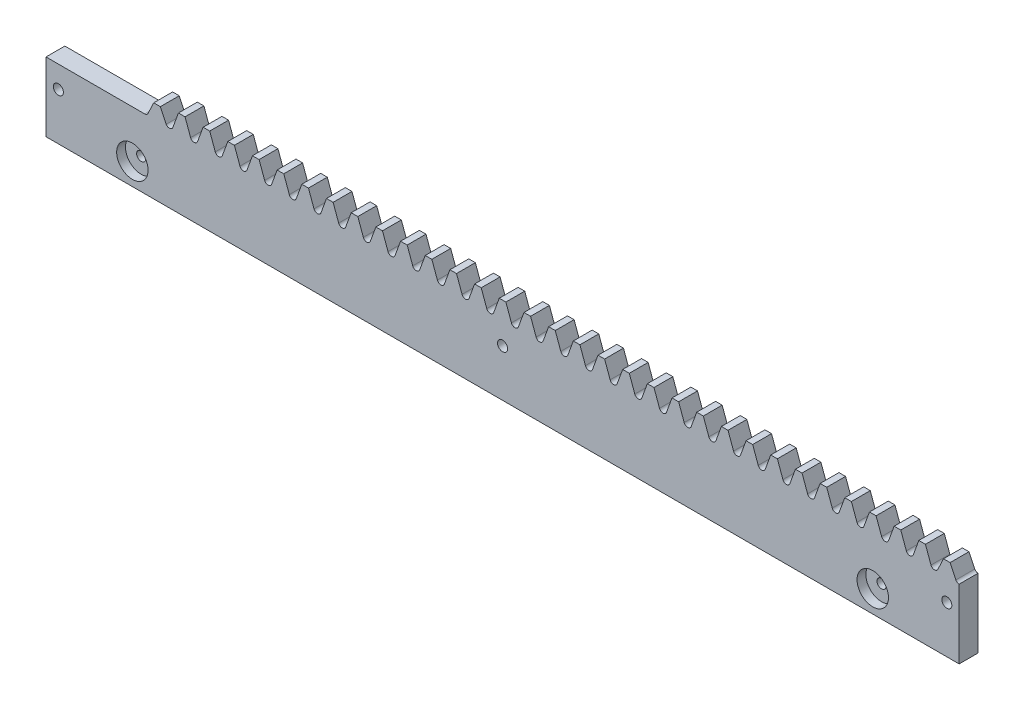
SolidWorks part; units mm, degrees
ref_plane "Plane1" through (0, 0, 0) normal (0, 0, 1) x (1, 0, 0)
ref_plane "Plane2" through (0, 0, 0) normal (0, 1, 0) x (1, 0, 0)
ref_plane "Plane3" through (0, 0, 0) normal (1, 0, 0) x (0, 0, -1)
sketch "Esquisse1" plane through (0, 0, 0) normal (0, 0, 1) x (1, 0, 0)
  line L0 (-11.781, 22) -> (19.635, 22)
  line L1 (23.5619, 29.1362) -> (23.5619, 19.2192) construction
  line L2 (-16.2297, 22) -> (24.6155, 22) construction
  line L3 (18.2522, 26.5) -> (283.3605, 26.5) construction
  line L4 (22.5084, 28.8854) -> (22.5084, 23.1798) construction
  line L5 (22.5084, 26.5) -> (20.6365, 22.5562)
  line L6 (24.6155, 26.5) -> (26.4874, 22.5562)
  line L7 (-29.4776, 0) -> (286.0574, 0) construction
  line L8 (22.5084, 26.5) -> (24.6155, 26.5)
  line L10 (275.9429, 26.742) -> (275.9429, 19.9201) construction
  line L11 (273.8358, 26.742) -> (273.8358, 19.9201) construction
  line L12 (273.8358, 26.5) -> (272.0069, 22.6314)
  line L13 (275.9429, 26.5) -> (277.7718, 22.6314)
  line L14 (273.8358, 26.5) -> (275.9429, 26.5)
  line L20 (28.5976, 22.7763) -> (30.3624, 27.625)
  line L21 (30.3624, 27.625) -> (32.4695, 27.625)
  line L22 (34.2343, 22.7763) -> (32.4695, 27.625)
  line L23 (36.4515, 22.7763) -> (38.2163, 27.625)
  line L24 (38.2163, 27.625) -> (40.3235, 27.625)
  line L25 (42.0883, 22.7763) -> (40.3235, 27.625)
  line L26 (44.3055, 22.7763) -> (46.0703, 27.625)
  line L27 (46.0703, 27.625) -> (48.1775, 27.625)
  line L28 (49.9423, 22.7763) -> (48.1775, 27.625)
  line L29 (52.1595, 22.7763) -> (53.9243, 27.625)
  line L30 (53.9243, 27.625) -> (56.0314, 27.625)
  line L31 (57.7962, 22.7763) -> (56.0314, 27.625)
  line L32 (60.0135, 22.7763) -> (61.7783, 27.625)
  line L33 (61.7783, 27.625) -> (63.8854, 27.625)
  line L34 (65.6502, 22.7763) -> (63.8854, 27.625)
  line L35 (67.8675, 22.7763) -> (69.6323, 27.625)
  line L36 (69.6323, 27.625) -> (71.7394, 27.625)
  line L37 (73.5042, 22.7763) -> (71.7394, 27.625)
  line L38 (75.7215, 22.7763) -> (77.4862, 27.625)
  line L39 (77.4862, 27.625) -> (79.5934, 27.625)
  line L40 (81.3582, 22.7763) -> (79.5934, 27.625)
  line L41 (83.5754, 22.7763) -> (85.3402, 27.625)
  line L42 (85.3402, 27.625) -> (87.4474, 27.625)
  line L43 (89.2122, 22.7763) -> (87.4474, 27.625)
  line L44 (91.4294, 22.7763) -> (93.1942, 27.625)
  line L45 (93.1942, 27.625) -> (95.3013, 27.625)
  line L46 (97.0661, 22.7763) -> (95.3013, 27.625)
  line L47 (99.2834, 22.7763) -> (101.0482, 27.625)
  line L48 (101.0482, 27.625) -> (103.1553, 27.625)
  line L49 (104.9201, 22.7763) -> (103.1553, 27.625)
  line L50 (107.1374, 22.7763) -> (108.9022, 27.625)
  line L51 (108.9022, 27.625) -> (111.0093, 27.625)
  line L52 (112.7741, 22.7763) -> (111.0093, 27.625)
  line L53 (114.9914, 22.7763) -> (116.7562, 27.625)
  line L54 (116.7562, 27.625) -> (118.8633, 27.625)
  line L55 (120.6281, 22.7763) -> (118.8633, 27.625)
  line L56 (122.8453, 22.7763) -> (124.6101, 27.625)
  line L57 (124.6101, 27.625) -> (126.7173, 27.625)
  line L58 (128.4821, 22.7763) -> (126.7173, 27.625)
  line L59 (130.6993, 22.7763) -> (132.4641, 27.625)
  line L60 (132.4641, 27.625) -> (134.5713, 27.625)
  line L61 (136.3361, 22.7763) -> (134.5713, 27.625)
  line L62 (138.5533, 22.7763) -> (140.3181, 27.625)
  line L63 (140.3181, 27.625) -> (142.4252, 27.625)
  line L64 (144.19, 22.7763) -> (142.4252, 27.625)
  line L65 (146.4073, 22.7763) -> (148.1721, 27.625)
  line L66 (148.1721, 27.625) -> (150.2792, 27.625)
  line L67 (152.044, 22.7763) -> (150.2792, 27.625)
  line L68 (154.2613, 22.7763) -> (156.0261, 27.625)
  line L69 (156.0261, 27.625) -> (158.1332, 27.625)
  line L70 (159.898, 22.7763) -> (158.1332, 27.625)
  line L71 (162.1153, 22.7763) -> (163.88, 27.625)
  line L72 (163.88, 27.625) -> (165.9872, 27.625)
  line L73 (167.752, 22.7763) -> (165.9872, 27.625)
  line L74 (169.9692, 22.7763) -> (171.734, 27.625)
  line L75 (171.734, 27.625) -> (173.8412, 27.625)
  line L76 (175.606, 22.7763) -> (173.8412, 27.625)
  line L77 (177.8232, 22.7763) -> (179.588, 27.625)
  line L78 (179.588, 27.625) -> (181.6951, 27.625)
  line L79 (183.4599, 22.7763) -> (181.6951, 27.625)
  line L80 (185.6772, 22.7763) -> (187.442, 27.625)
  line L81 (187.442, 27.625) -> (189.5491, 27.625)
  line L82 (191.3139, 22.7763) -> (189.5491, 27.625)
  line L83 (193.5312, 22.7763) -> (195.296, 27.625)
  line L84 (195.296, 27.625) -> (197.4031, 27.625)
  line L85 (199.1679, 22.7763) -> (197.4031, 27.625)
  line L86 (201.3852, 22.7763) -> (203.15, 27.625)
  line L87 (203.15, 27.625) -> (205.2571, 27.625)
  line L88 (207.0219, 22.7763) -> (205.2571, 27.625)
  line L89 (209.2391, 22.7763) -> (211.0039, 27.625)
  line L90 (211.0039, 27.625) -> (213.1111, 27.625)
  line L91 (214.8759, 22.7763) -> (213.1111, 27.625)
  line L92 (217.0931, 22.7763) -> (218.8579, 27.625)
  line L93 (218.8579, 27.625) -> (220.9651, 27.625)
  line L94 (222.7298, 22.7763) -> (220.9651, 27.625)
  line L95 (224.9471, 22.7763) -> (226.7119, 27.625)
  line L96 (226.7119, 27.625) -> (228.819, 27.625)
  line L97 (230.5838, 22.7763) -> (228.819, 27.625)
  line L98 (232.8011, 22.7763) -> (234.5659, 27.625)
  line L99 (234.5659, 27.625) -> (236.673, 27.625)
  line L100 (238.4378, 22.7763) -> (236.673, 27.625)
  line L101 (240.6551, 22.7763) -> (242.4199, 27.625)
  line L102 (242.4199, 27.625) -> (244.527, 27.625)
  line L103 (246.2918, 22.7763) -> (244.527, 27.625)
  line L104 (248.509, 22.7763) -> (250.2738, 27.625)
  line L105 (250.2738, 27.625) -> (252.381, 27.625)
  line L106 (254.1458, 22.7763) -> (252.381, 27.625)
  line L107 (256.363, 22.7763) -> (258.1278, 27.625)
  line L108 (258.1278, 27.625) -> (260.235, 27.625)
  line L109 (261.9998, 22.7763) -> (260.235, 27.625)
  line L110 (264.217, 22.7763) -> (265.9818, 27.625)
  line L111 (265.9818, 27.625) -> (268.0889, 27.625)
  line L112 (269.8537, 22.7763) -> (268.0889, 27.625)
  line L113 (-11.781, 27.0667) -> (-11.781, -40.6674) construction
  line L114 (19.635, 37.0607) -> (19.635, -15.8181) construction
  line L115 (283.3605, 22) -> (228.0591, 22) construction
  line L116 (278.8163, 26.742) -> (278.8163, -7.4189) construction
  line L118 (-11.781, 22) -> (-11.781, 0)
  line L121 (278.8163, 22) -> (278.8163, 0)
  line L131 (278.8163, 0) -> (-11.781, 0)
  line L132 (133.5177, 28.2837) -> (133.5177, 9.5143) construction
  line L133 (130.5371, 22) -> (141.4123, 22) construction
  line L134 (-45.8284, 15) -> (286.0574, 15) construction
  line L135 (-7.854, 23.9583) -> (-7.854, 12.1613) construction
  line L136 (274.8894, 25.9335) -> (274.8894, 12.5592) construction
  line L137 (-2.8184, 22.7763) -> (-1.0536, 27.625) [skipped]
  line L138 (-1.0536, 27.625) -> (1.0536, 27.625) [skipped]
  line L139 (2.8184, 22.7763) -> (1.0536, 27.625) [skipped]
  line L140 (5.0356, 22.7763) -> (6.8004, 27.625) [skipped]
  line L141 (6.8004, 27.625) -> (8.9076, 27.625) [skipped]
  line L142 (10.6723, 22.7763) -> (8.9076, 27.625) [skipped]
  line L143 (12.8896, 22.7763) -> (14.6544, 27.625) [skipped]
  line L144 (14.6544, 27.625) -> (16.7615, 27.625) [skipped]
  line L145 (18.5263, 22.7763) -> (16.7615, 27.625) [skipped]
  line L146 (22.5084, 27.625) -> (24.6155, 27.625) [skipped]
  line L147 (26.3803, 22.7763) -> (24.6155, 27.625) [skipped]
  line L148 (20.7436, 22.7763) -> (22.5084, 27.625) [skipped]
  line L149 (273.8358, 27.625) -> (275.9429, 27.625) [skipped]
  line L150 (277.7077, 22.7763) -> (275.9429, 27.625) [skipped]
  line L151 (272.071, 22.7763) -> (273.8358, 27.625) [skipped]
  arc A7 (19.635, 22) -> (20.6365, 22.5562) centre (19.635, 23.1798) ccw
  arc A8 (27.4889, 22) -> (26.4874, 22.5562) centre (27.4889, 23.1798) cw
  arc A9 (27.4889, 22) -> (28.5976, 22.7763) centre (27.4889, 23.1798) ccw
  arc A10 (35.3429, 22) -> (34.2343, 22.7763) centre (35.3429, 23.1798) cw
  arc A11 (35.3429, 22) -> (36.4515, 22.7763) centre (35.3429, 23.1798) ccw
  arc A12 (43.1969, 22) -> (42.0883, 22.7763) centre (43.1969, 23.1798) cw
  arc A13 (43.1969, 22) -> (44.3055, 22.7763) centre (43.1969, 23.1798) ccw
  arc A14 (51.0509, 22) -> (49.9423, 22.7763) centre (51.0509, 23.1798) cw
  arc A15 (51.0509, 22) -> (52.1595, 22.7763) centre (51.0509, 23.1798) ccw
  arc A16 (58.9049, 22) -> (57.7962, 22.7763) centre (58.9049, 23.1798) cw
  arc A17 (58.9049, 22) -> (60.0135, 22.7763) centre (58.9049, 23.1798) ccw
  arc A18 (66.7588, 22) -> (65.6502, 22.7763) centre (66.7588, 23.1798) cw
  arc A19 (66.7588, 22) -> (67.8675, 22.7763) centre (66.7588, 23.1798) ccw
  arc A20 (74.6128, 22) -> (73.5042, 22.7763) centre (74.6128, 23.1798) cw
  arc A21 (74.6128, 22) -> (75.7215, 22.7763) centre (74.6128, 23.1798) ccw
  arc A22 (82.4668, 22) -> (81.3582, 22.7763) centre (82.4668, 23.1798) cw
  arc A23 (82.4668, 22) -> (83.5754, 22.7763) centre (82.4668, 23.1798) ccw
  arc A24 (90.3208, 22) -> (89.2122, 22.7763) centre (90.3208, 23.1798) cw
  arc A25 (90.3208, 22) -> (91.4294, 22.7763) centre (90.3208, 23.1798) ccw
  arc A26 (98.1748, 22) -> (97.0661, 22.7763) centre (98.1748, 23.1798) cw
  arc A27 (98.1748, 22) -> (99.2834, 22.7763) centre (98.1748, 23.1798) ccw
  arc A28 (106.0288, 22) -> (104.9201, 22.7763) centre (106.0288, 23.1798) cw
  arc A29 (106.0288, 22) -> (107.1374, 22.7763) centre (106.0288, 23.1798) ccw
  arc A30 (113.8827, 22) -> (112.7741, 22.7763) centre (113.8827, 23.1798) cw
  arc A31 (113.8827, 22) -> (114.9914, 22.7763) centre (113.8827, 23.1798) ccw
  arc A32 (121.7367, 22) -> (120.6281, 22.7763) centre (121.7367, 23.1798) cw
  arc A33 (121.7367, 22) -> (122.8453, 22.7763) centre (121.7367, 23.1798) ccw
  arc A34 (129.5907, 22) -> (128.4821, 22.7763) centre (129.5907, 23.1798) cw
  arc A35 (129.5907, 22) -> (130.6993, 22.7763) centre (129.5907, 23.1798) ccw
  arc A36 (137.4447, 22) -> (136.3361, 22.7763) centre (137.4447, 23.1798) cw
  arc A37 (137.4447, 22) -> (138.5533, 22.7763) centre (137.4447, 23.1798) ccw
  arc A38 (145.2987, 22) -> (144.19, 22.7763) centre (145.2987, 23.1798) cw
  arc A39 (145.2987, 22) -> (146.4073, 22.7763) centre (145.2987, 23.1798) ccw
  arc A40 (153.1526, 22) -> (152.044, 22.7763) centre (153.1526, 23.1798) cw
  arc A41 (153.1526, 22) -> (154.2613, 22.7763) centre (153.1526, 23.1798) ccw
  arc A42 (161.0066, 22) -> (159.898, 22.7763) centre (161.0066, 23.1798) cw
  arc A43 (161.0066, 22) -> (162.1153, 22.7763) centre (161.0066, 23.1798) ccw
  arc A44 (168.8606, 22) -> (167.752, 22.7763) centre (168.8606, 23.1798) cw
  arc A45 (168.8606, 22) -> (169.9692, 22.7763) centre (168.8606, 23.1798) ccw
  arc A46 (176.7146, 22) -> (175.606, 22.7763) centre (176.7146, 23.1798) cw
  arc A47 (176.7146, 22) -> (177.8232, 22.7763) centre (176.7146, 23.1798) ccw
  arc A48 (184.5686, 22) -> (183.4599, 22.7763) centre (184.5686, 23.1798) cw
  arc A49 (184.5686, 22) -> (185.6772, 22.7763) centre (184.5686, 23.1798) ccw
  arc A50 (192.4226, 22) -> (191.3139, 22.7763) centre (192.4226, 23.1798) cw
  arc A51 (192.4226, 22) -> (193.5312, 22.7763) centre (192.4226, 23.1798) ccw
  arc A52 (200.2765, 22) -> (199.1679, 22.7763) centre (200.2765, 23.1798) cw
  arc A53 (200.2765, 22) -> (201.3852, 22.7763) centre (200.2765, 23.1798) ccw
  arc A54 (208.1305, 22) -> (207.0219, 22.7763) centre (208.1305, 23.1798) cw
  arc A55 (208.1305, 22) -> (209.2391, 22.7763) centre (208.1305, 23.1798) ccw
  arc A56 (215.9845, 22) -> (214.8759, 22.7763) centre (215.9845, 23.1798) cw
  arc A57 (215.9845, 22) -> (217.0931, 22.7763) centre (215.9845, 23.1798) ccw
  arc A58 (223.8385, 22) -> (222.7298, 22.7763) centre (223.8385, 23.1798) cw
  arc A59 (223.8385, 22) -> (224.9471, 22.7763) centre (223.8385, 23.1798) ccw
  arc A60 (231.6925, 22) -> (230.5838, 22.7763) centre (231.6925, 23.1798) cw
  arc A61 (231.6925, 22) -> (232.8011, 22.7763) centre (231.6925, 23.1798) ccw
  arc A62 (239.5464, 22) -> (238.4378, 22.7763) centre (239.5464, 23.1798) cw
  arc A63 (239.5464, 22) -> (240.6551, 22.7763) centre (239.5464, 23.1798) ccw
  arc A64 (247.4004, 22) -> (246.2918, 22.7763) centre (247.4004, 23.1798) cw
  arc A65 (247.4004, 22) -> (248.509, 22.7763) centre (247.4004, 23.1798) ccw
  arc A66 (255.2544, 22) -> (254.1458, 22.7763) centre (255.2544, 23.1798) cw
  arc A67 (255.2544, 22) -> (256.363, 22.7763) centre (255.2544, 23.1798) ccw
  arc A68 (263.1084, 22) -> (261.9998, 22.7763) centre (263.1084, 23.1798) cw
  arc A69 (263.1084, 22) -> (264.217, 22.7763) centre (263.1084, 23.1798) ccw
  arc A70 (270.9624, 22) -> (269.8537, 22.7763) centre (270.9624, 23.1798) cw
  arc A72 (270.9624, 22) -> (272.0069, 22.6314) centre (270.9624, 23.1798) ccw
  arc A79 (278.8163, 22) -> (277.7718, 22.6314) centre (278.8163, 23.1798) cw
  circle A80 centre (133.5177, 15) radius 1.6
  circle A81 centre (-7.854, 15) radius 1.6
  circle A82 centre (274.8894, 15) radius 1.6
  arc A83 (19.635, 22) -> (18.5263, 22.7763) centre (19.635, 23.1798) cw [skipped]
  arc A84 (-3.927, 22) -> (-2.8184, 22.7763) centre (-3.927, 23.1798) ccw [skipped]
  arc A85 (3.927, 22) -> (2.8184, 22.7763) centre (3.927, 23.1798) cw [skipped]
  arc A86 (3.927, 22) -> (5.0356, 22.7763) centre (3.927, 23.1798) ccw [skipped]
  arc A87 (11.781, 22) -> (10.6723, 22.7763) centre (11.781, 23.1798) cw [skipped]
  arc A88 (11.781, 22) -> (12.8896, 22.7763) centre (11.781, 23.1798) ccw [skipped]
  dimension "D2" = 4.5
  dimension "D1" = 7
extrude "Extrusion1" add sketch "Esquisse1" along normal blind 6
sketch "Esquisse4" plane through (0, 0, 6) normal (0, 0, 1) x (1, 0, 0)
  line L0 (15.708, 31.1875) -> (15.708, -14.7899) construction
  line L1 (6.9611, 7) -> (270.7775, 7) construction
  line L2 (251.3274, 30.2531) -> (251.3274, -5.0048) construction
  circle A0 centre (15.708, 7) radius 5
  circle A2 centre (251.3274, 7) radius 5
extrude "Enlèv. mat.-Extru.2" cut sketch "Esquisse4" against normal blind 2.8
sketch "Esquisse5" plane through (0, 0, 3.2) normal (0, 0, 1) x (1, 0, 0)
  line L0 (15.708, 33.4411) -> (15.708, -6.3197) construction
  line L1 (9.4058, 7) -> (272.7995, 7) construction
  line L2 (251.3274, 30.3305) -> (251.3274, -6.3197) construction
  circle A0 centre (15.708, 7) radius 1.45
  circle A1 centre (251.3274, 7) radius 1.45
extrude "Enlèv. mat.-Extru.3" cut sketch "Esquisse5" against normal blind 2.5
